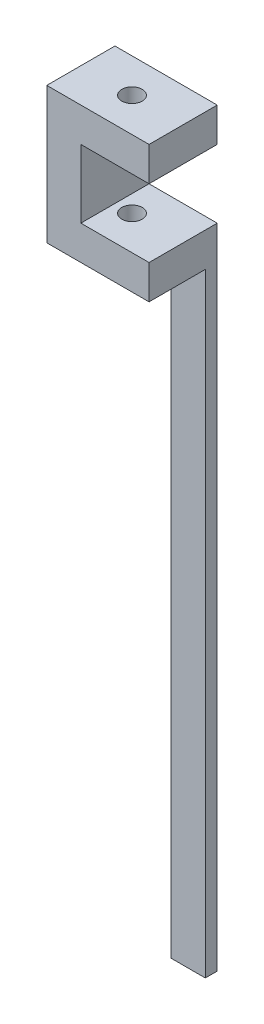
SolidWorks part; units mm, degrees
ref_plane "Front Plane" through (0, 0, 0) normal (0, 0, 1) x (1, 0, 0)
ref_plane "Top Plane" through (0, 0, 0) normal (0, 1, 0) x (1, 0, 0)
ref_plane "Right Plane" through (0, 0, 0) normal (1, 0, 0) x (0, 0, -1)
sketch "Sketch1" plane through (0, 0, 0) normal (0, 0, 1) x (1, 0, 0)
  line L9 (0, 10.8119) -> (0, -9.1881)
  line L10 (0, -9.1881) -> (15, -9.1881)
  line L11 (15, -9.1881) -> (15, -4.1881)
  line L12 (15, -4.1881) -> (5, -4.1881)
  line L13 (0, 10.8119) -> (15, 10.8119)
  line L14 (15, 10.8119) -> (15, 5.8119)
  line L15 (15, 5.8119) -> (5, 5.8119)
  line L16 (5, 5.8119) -> (5, -4.1881)
  point P3 (0, 0.8119)
  dimension "D1" = 20
  dimension "D2" = 10
  dimension "D3" = 5
  dimension "D4" = 5
  dimension "D5" = 10
  dimension "D6" = 15
extrude "Boss-Extrude1" add sketch "Sketch1" along normal blind 10
sketch "Sketch3" plane through (0, -9.1881, 0) normal (0, -1, 0) x (-1, 0, 0)
  line L1 (-15, 0) -> (-10, 0)
  line L2 (-15, 0) -> (-15, -1.75)
  line L3 (-15, -1.75) -> (-10, -1.75)
  line L4 (-10, 0) -> (-10, -1.75)
  dimension "D1" = 5
  dimension "D2" = 1.75
extrude "Boss-Extrude2" add sketch "Sketch3" along normal blind 90
sketch "Sketch4" plane through (0, 10.8119, 0) normal (0, 1, 0) x (1, 0, 0)
  line L0 (7.5, 0) -> (7.5, -10) construction
  line L1 (15, 0) -> (0, 0) construction
  line L2 (15, -10) -> (0, -10) construction
  circle A0 centre (7.5, -5) radius 1.5
  dimension "D1" = 3
extrude "Cut-Extrude1" cut sketch "Sketch4" against normal through all
